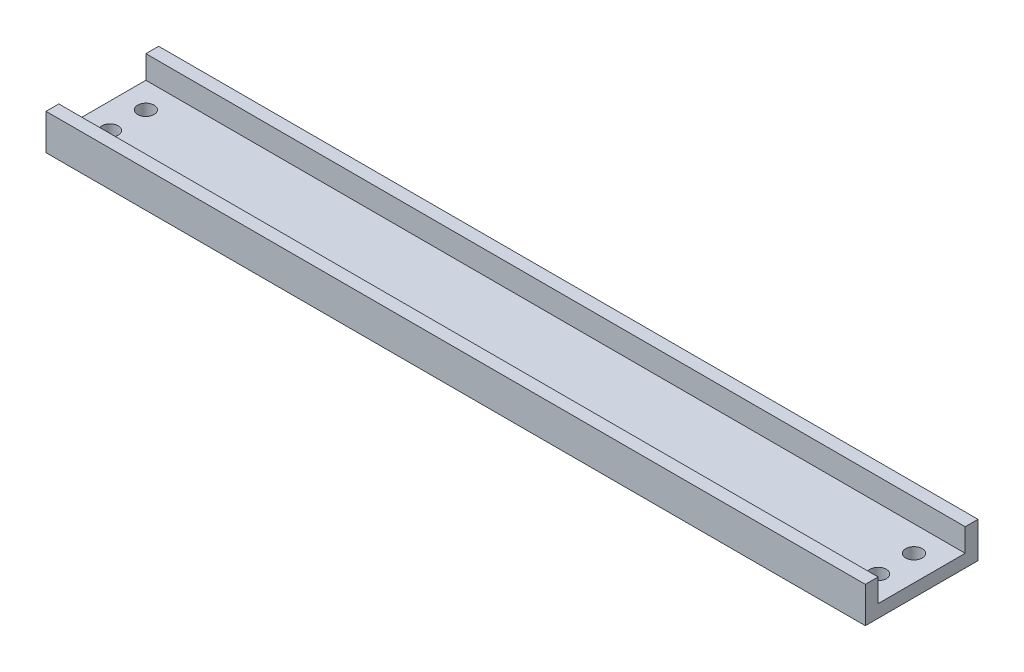
SolidWorks part; units mm, degrees
ref_plane "Front Plane" through (0, 0, 0) normal (0, 0, 1) x (1, 0, 0)
ref_plane "Top Plane" through (0, 0, 0) normal (0, 1, 0) x (1, 0, 0)
ref_plane "Right Plane" through (0, 0, 0) normal (1, 0, 0) x (0, 0, -1)
sketch "Sketch1" plane through (0, 0, 0) normal (0, 1, 0) x (1, 0, 0)
  line L1 (-81.0811, 4.1441) -> (78.9189, 4.1441)
  line L2 (-81.0811, 4.1441) -> (-81.0811, -17.8559)
  line L3 (-81.0811, -17.8559) -> (78.9189, -17.8559)
  line L4 (78.9189, 4.1441) -> (78.9189, -17.8559)
  line L5 (-81.0811, 4.1441) -> (78.9189, -17.8559) construction
  line L6 (-81.0811, -17.8559) -> (78.9189, 4.1441) construction
  point P0 (-1.0811, -6.8559)
  dimension "D1" = 160
  dimension "D2" = 22
extrude "Boss-Extrude1" add sketch "Sketch1" along normal mid plane 2.5
sketch "Sketch2" plane through (0, 1.25, 0) normal (0, 1, 0) x (1, 0, 0)
  line L0 (78.9189, 4.1441) -> (-81.0811, 4.1441) construction
  line L1 (78.9189, 4.1441) -> (-81.0811, 4.1441)
  line L2 (-81.0811, -17.8559) -> (78.9189, -17.8559) construction
  line L3 (-81.0811, -17.8559) -> (78.9189, -17.8559)
  line L4 (78.9189, 1.6441) -> (-81.0811, 1.6441)
  line L5 (-81.0811, -15.3559) -> (78.9189, -15.3559)
  line L6 (78.9189, 4.1441) -> (78.9189, 1.6441)
  line L7 (-81.0811, 4.1441) -> (-81.0811, 1.6441)
  line L8 (-81.0811, -17.8559) -> (-81.0811, -15.3559)
  line L9 (78.9189, -17.8559) -> (78.9189, -15.3559)
  dimension "D1" = 2.5
extrude "Boss-Extrude2" add sketch "Sketch2" along normal blind 4.5
sketch "Sketch3" plane through (0, 0, -4.1441) normal (0, 0, -1) x (-1, 0, 0)
  line L0 (-78.9189, 5.75) -> (-78.9189, -1.25) construction
  line L1 (-78.9189, 5.75) -> (-78.9189, -1.25)
sketch "Sketch4" plane through (0, 1.25, 0) normal (0, 1, 0) x (1, 0, 0)
  line L0 (78.9189, -15.3559) -> (78.9189, 1.6441) construction
  line L1 (78.9189, -15.3559) -> (-81.0811, -15.3559) construction
  line L2 (-81.0811, 1.6441) -> (78.9189, 1.6441) construction
  line L3 (-1.0811, 4.1441) -> (-1.0811, -17.8559) construction
  line L4 (78.9189, 4.1441) -> (-81.0811, 4.1441) construction
  line L5 (-81.0811, -17.8559) -> (78.9189, -17.8559) construction
  circle A0 centre (73.9189, -3.3559) radius 1.6
  circle A1 centre (73.9189, -10.3559) radius 1.6
  circle A2 centre (-76.0811, -10.3559) radius 1.6
  circle A3 centre (-76.0811, -3.3559) radius 1.6
  dimension "D1" = 3.2
  dimension "D2" = 3.2
  dimension "D3" = 5
  dimension "D4" = 5
  dimension "D5" = 5
  dimension "D6" = 5
extrude "Cut-Extrude1" cut sketch "Sketch4" against normal through all
sketch "Sketch5" plane through (0, 1.25, 0) normal (0, 1, 0) x (1, 0, 0)
  line L0 (-81.0811, 1.6441) -> (-81.0811, -15.3559) construction
  line L1 (-81.0811, 1.6441) -> (-81.0811, -15.3559) construction
  line L2 (-81.0811, 1.6441) -> (78.9189, 1.6441) construction
  dimension "D1" = 17
